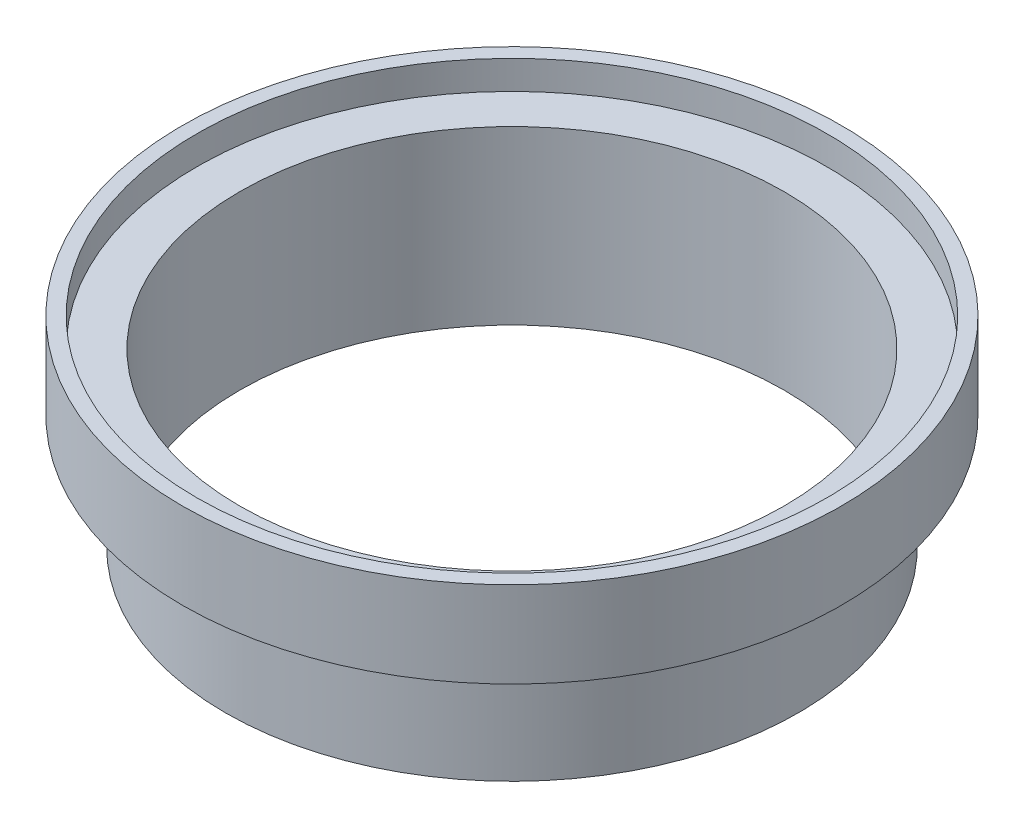
SolidWorks part; units mm, degrees
material "6061-T6 (SS)"
ref_plane "Front Plane" through (0, 0, 0) normal (0, 0, 1) x (1, 0, 0)
ref_plane "Top Plane" through (0, 0, 0) normal (0, 1, 0) x (1, 0, 0)
ref_plane "Right Plane" through (0, 0, 0) normal (1, 0, 0) x (0, 0, -1)
ref_axis "Axis1" through (0, 65.0522, 0) along (0, -1, 0)
sketch "Sketch1" plane through (0, 0, 0) normal (0, 0, 1) x (1, 0, 0)
  line L0 (-60.325, 0) -> (-60.325, 38.1)
  line L1 (41.7635, 0) -> (-41.7635, 0) construction
  line L2 (0, 65.0522) -> (0, -55) construction
  line L3 (-60.325, 0) -> (-63.5, 0)
  line L4 (-63.5, 0) -> (-63.5, 25.4)
  line L5 (-63.5, 25.4) -> (-73.025, 25.4)
  line L6 (-73.025, 25.4) -> (-73.025, 44.45)
  line L7 (-73.025, 44.45) -> (-69.85, 44.45)
  line L8 (-69.85, 44.45) -> (-69.85, 38.1)
  line L9 (-69.85, 38.1) -> (-60.325, 38.1)
  dimension "D1" = 60.325
  dimension "D2" = 38.1
  dimension "D3" = 3.175
  dimension "D4" = 9.525
  dimension "D5" = 25.4
  dimension "D6" = 3.175
  dimension "D7" = 19.05
revolve "Revolve1" add sketch "Sketch1" angle 360 about axis through (0, 65.0522, 0) along (0, -1, 0)
